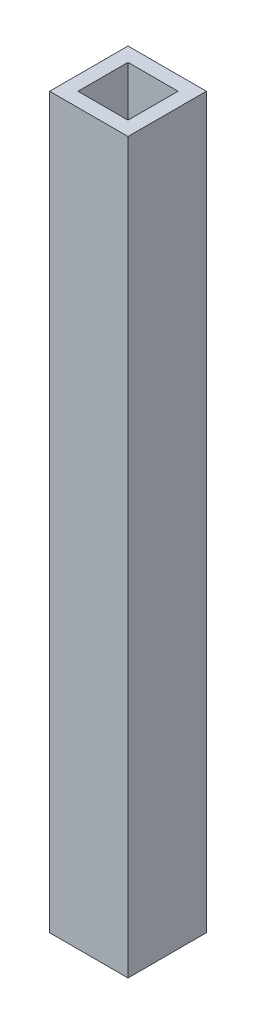
SolidWorks part; units mm, degrees
ref_plane "Front Plane" through (0, 0, 0) normal (0, 0, 1) x (1, 0, 0)
ref_plane "Top Plane" through (0, 0, 0) normal (0, 1, 0) x (1, 0, 0)
ref_plane "Right Plane" through (0, 0, 0) normal (1, 0, 0) x (0, 0, -1)
sketch "Sketch1" plane through (0, 0, 0) normal (0, 1, 0) x (1, 0, 0)
  line L1 (-5.969, 5.969) -> (5.969, 5.969)
  line L2 (-5.969, 5.969) -> (-5.969, -5.969)
  line L3 (-5.969, -5.969) -> (5.969, -5.969)
  line L4 (5.969, 5.969) -> (5.969, -5.969)
  line L9 (-5.969, 5.969) -> (5.969, -5.969) construction
  line L10 (-5.969, -5.969) -> (5.969, 5.969) construction
  point P0 (0, 0)
  dimension "D1" = 11.938
  dimension "D2" = 11.938
extrude "Boss-Extrude1" add sketch "Sketch1" along normal blind 213.106
sketch "Sketch2" plane through (0, 213.106, 0) normal (0, 1, 0) x (1, 0, 0)
  circle A0 centre (0, 0) radius 3.6805
  dimension "D1" = 7.3609
extrude "Boss-Extrude2" add sketch "Sketch2" along normal blind 22.225
sketch "Sketch3" plane through (0, 0, 0) normal (0, -1, 0) x (-1, 0, 0)
  circle A0 centre (0, 0) radius 4.0005
  dimension "D1" = 8.001
sketch "Sketch4" plane through (0, 235.331, 0) normal (0, 1, 0) x (1, 0, 0)
  line L1 (-2.286, 2.286) -> (2.286, 2.286)
  line L2 (-2.286, 2.286) -> (-2.286, -2.286)
  line L3 (-2.286, -2.286) -> (2.286, -2.286)
  line L4 (2.286, 2.286) -> (2.286, -2.286)
  line L5 (-2.286, 2.286) -> (2.286, -2.286) construction
  line L6 (-2.286, -2.286) -> (2.286, 2.286) construction
  point P0 (0, 0)
  dimension "D1" = 4.572
  dimension "D2" = 4.572
extrude "Boss-Extrude4" add sketch "Sketch4" along normal blind 15.24
sketch "Sketch5" plane through (0, 250.571, 0) normal (0, 1, 0) x (1, 0, 0)
  circle A0 centre (0, 0) radius 13.0511
extrude "Cut-Extrude1" cut sketch "Sketch5" against normal blind 139.573
sketch "Sketch6" plane through (0, 110.998, 0) normal (0, 1, 0) x (1, 0, 0)
  line L1 (-3.81, -3.81) -> (3.81, -3.81)
  line L2 (-3.81, -3.81) -> (-3.81, 3.81)
  line L3 (-3.81, 3.81) -> (3.81, 3.81)
  line L4 (3.81, -3.81) -> (3.81, 3.81)
  line L5 (-3.81, -3.81) -> (3.81, 3.81) construction
  line L6 (-3.81, 3.81) -> (3.81, -3.81) construction
  point P0 (0, 0)
  dimension "D1" = 7.62
  dimension "D2" = 7.62
extrude "Cut-Extrude2" cut sketch "Sketch6" against normal blind 12.7
extrude "Cut-Extrude4" cut sketch "Sketch3" against normal blind 14.2875 contours A0
